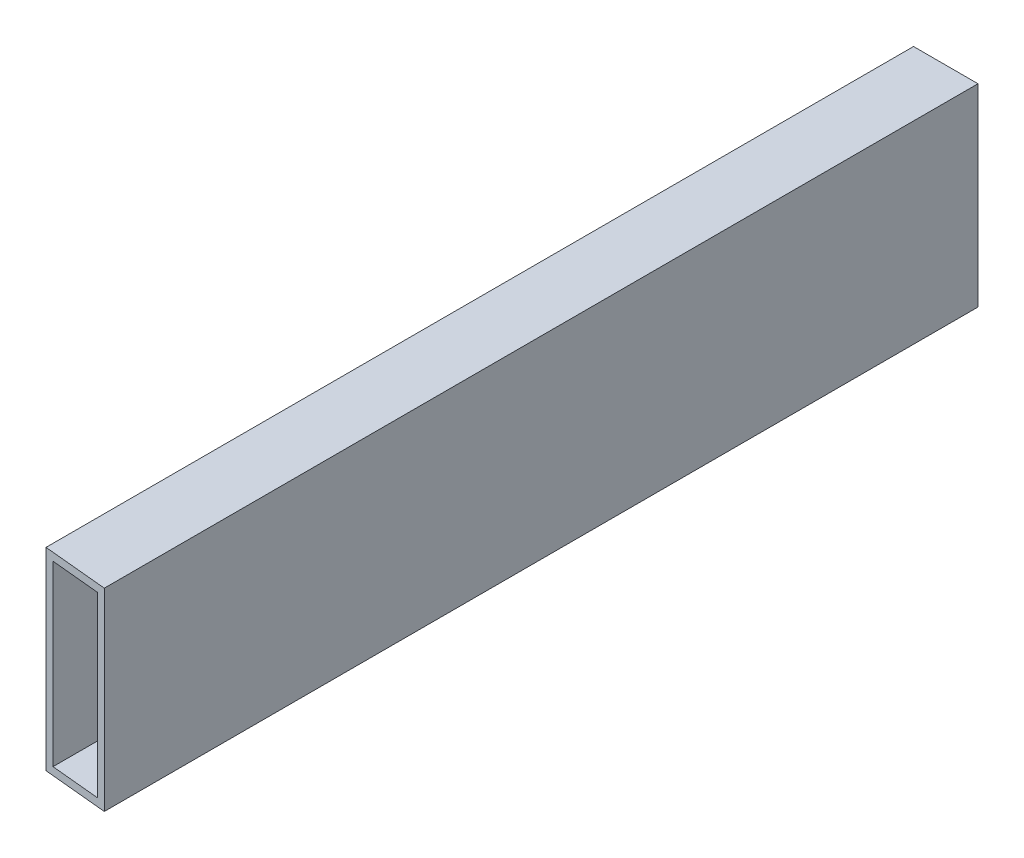
SolidWorks part; units mm, degrees
material "A500"
ref_plane "Front Plane" through (0, 0, 0) normal (0, 0, 1) x (1, 0, 0)
ref_plane "Top Plane" through (0, 0, 0) normal (0, 1, 0) x (1, 0, 0)
ref_plane "Right Plane" through (0, 0, 0) normal (1, 0, 0) x (0, 0, -1)
sketch "Sketch2" plane through (0, 0, 0) normal (0, 0, 1) x (1, 0, 0)
  line L0 (0, 0) -> (0, 38.1)
  line L1 (0, 38.1) -> (12.7, 38.1)
  line L2 (12.7, 38.1) -> (12.7, 0)
  line L3 (12.7, 0) -> (0, 0)
  line L4 (12.7, -38.1) -> (12.7, -35.052)
  line L5 (0, 0) -> (-12.7, 0)
  line L6 (0, 0) -> (0, -38.1)
  line L7 (0, -38.1) -> (-12.7, -38.1)
  line L8 (-12.7, 0) -> (-12.7, -38.1)
  line L9 (-12.7, -38.1) -> (12.7, -38.1)
  line L10 (-12.7, -38.1) -> (-12.7, 38.1)
  line L11 (-12.7, 38.1) -> (12.7, 38.1)
  line L12 (12.7, -38.1) -> (12.7, 38.1)
  line L13 (12.7, -35.052) -> (9.652, -35.052)
  line L14 (-12.7, 38.1) -> (-9.652, 38.1)
  line L15 (-9.652, 38.1) -> (-9.652, 35.052)
  line L17 (-9.652, 35.052) -> (9.652, 35.052)
  line L18 (-9.652, 35.052) -> (-9.652, -35.052)
  line L19 (-9.652, -35.052) -> (9.652, -35.052)
  line L20 (9.652, 35.052) -> (9.652, -35.052)
  dimension "D1" = 38.1
  dimension "D2" = 12.7
  dimension "D3" = 38.1
  dimension "D4" = 12.7
  dimension "D5" = 3.048
  dimension "D6" = 3.048
  dimension "D7" = 3.048
  dimension "D8" = 3.048
extrude "Boss-Extrude1" add sketch "Sketch2" along normal up to vertex (322.3727 mm away) contours L18 L15 L11 L10 L5 | L15 L17 L0 L11 | L17 L20 L3 L2 L1 L0 | L3 L20 L13 L12 | L19 L18 L5 L8 L7 L6 | L19 L6 L9 L4 L13
sketch "Sketch3" plane through (0, 0, 343) normal (0, 0, 1) x (1, 0, 0)
  line L1 (-12.7, 38.1) -> (12.7, 38.1)
  line L2 (-12.7, 38.1) -> (-12.7, -38.1)
  line L3 (-12.7, -38.1) -> (12.7, -38.1)
  line L4 (12.7, 38.1) -> (12.7, -38.1)
  line L5 (9.652, -35.052) -> (-9.652, -35.052)
  line L6 (9.652, -35.052) -> (9.652, 35.052)
  line L7 (9.652, 35.052) -> (-9.652, 35.052)
  line L8 (-9.652, -35.052) -> (-9.652, 35.052)
extrude "Boss-Extrude2" add sketch "Sketch3" along normal blind 50
sketch "Sketch4" plane through (0, 38.1, 0) normal (0, 1, 0) x (1, 0, 0)
  line L0 (94.3097, -352.0432) -> (-94.3097, -333.9568)
  line L1 (0, -293) -> (0, -343)
  line L3 (-9.5015, -392.0889) -> (0, -343)
  line L4 (-14.8, -419.4631) -> (0, -343) construction
  line L5 (0, -293) -> (94.3097, -352.0432)
  line L6 (-9.5015, -392.0889) -> (94.3097, -352.0432)
  line L7 (94.3097, -352.0432) -> (-94.3097, -333.9568)
  line L8 (94.3097, -352.0432) -> (89.3519, -403.7472)
  line L9 (-94.3097, -333.9568) -> (-99.2675, -385.6607)
  line L10 (89.3519, -403.7472) -> (-99.2675, -385.6607)
  line M7 (-12.7, 0) -> (-12.7, -393)
  line M8 (-12.7, -393) -> (12.7, -393)
  line M9 (12.7, -393) -> (12.7, 0)
  dimension "D1" = 50
  dimension "D2" = 50
extrude "Cut-Extrude1" cut sketch "Sketch4" against normal through all both and the other way through all contours L10 L8 L6 L0 L9 M9 M8 M7 | L6 L0 M9 | L3 L6 L0 M9 | L6 L3 L0 M7 M8 M9
equation "\"D3@Sketch2\"=\"D1@Sketch2\""
equation "\"D4@Sketch2\"=\"D2@Sketch2\""
